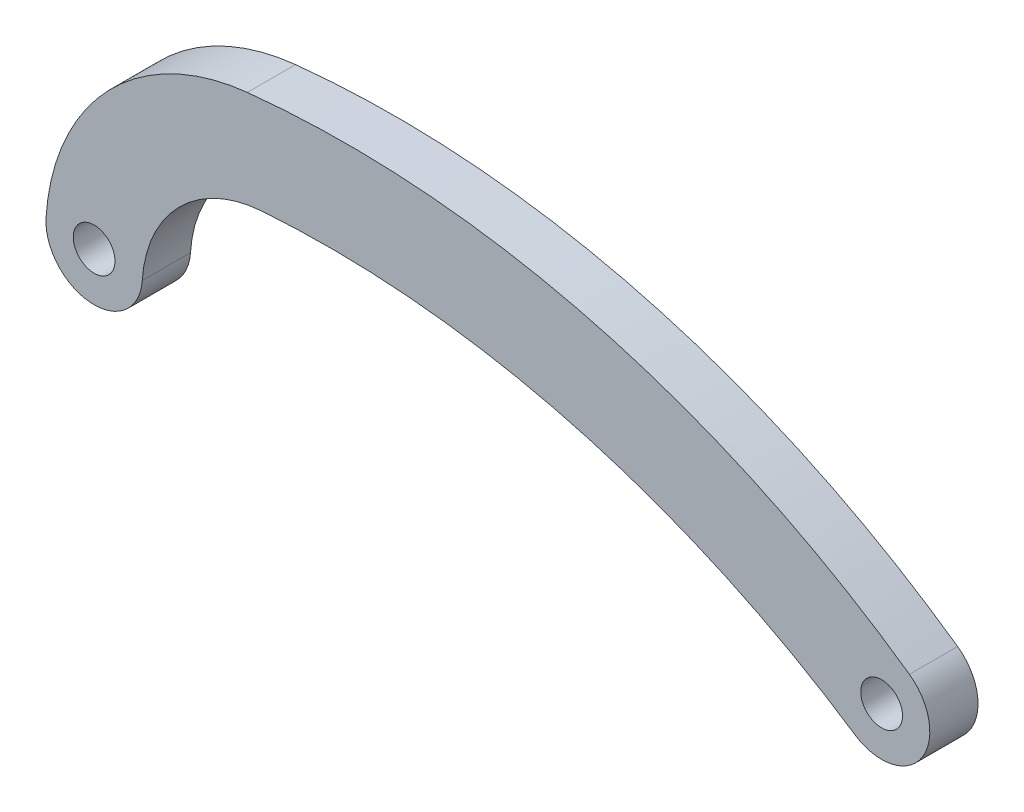
SolidWorks part; units mm, degrees
ref_plane "정면" through (0, 0, 0) normal (0, 0, 1) x (1, 0, 0)
ref_plane "윗면" through (0, 0, 0) normal (0, 1, 0) x (1, 0, 0)
ref_plane "우측면" through (0, 0, 0) normal (1, 0, 0) x (0, 0, -1)
sketch "스케치1" plane through (0, 0, 0) normal (0, 0, 1) x (1, 0, 0)
  arc A2 (5.9081, 12.1254) -> (-6.618, -0.8901) centre (7.3524, -1.7999) ccw
  arc A3 (-6.618, -0.8901) -> (-0.6307, -1.28) centre (-3.6244, -1.0851) ccw
  arc A5 (6.7752, 6.1793) -> (-0.6307, -1.28) centre (7.3524, -1.7999) ccw
  arc A6 (43.7094, -3.5798) -> (47.1047, 1.3665) centre (45.3756, -1.0851) ccw
  arc A10 (43.7094, -3.5798) -> (6.7752, 6.1793) centre (11.0213, -52.521) ccw
  arc A11 (47.1047, 1.3665) -> (5.9081, 12.1254) centre (12.1626, -48.1775) ccw
  circle A12 centre (-3.6244, -1.0851) radius 1.5
  circle A13 centre (45.3756, -1.0851) radius 1.5
  dimension "D1" = 6
  dimension "D2" = 49
  dimension "D3" = 28
  dimension "D4" = 6
  dimension "D5" = 3
  dimension "D6" = 3
extrude "보스-돌출1" add sketch "스케치1" along normal blind 3 contours A11 A2 A3 A5 A10 A6
sketch "스케치2" plane through (0, 0, 3) normal (0, 0, 1) x (1, 0, 0)
  circle A0 centre (-3.6244, -1.0851) radius 1.3
  circle A1 centre (45.3756, -1.0851) radius 1.3
  dimension "D1" = 2.6
  dimension "D2" = 2.6
extrude "컷-돌출1" cut sketch "스케치2" against normal through all
